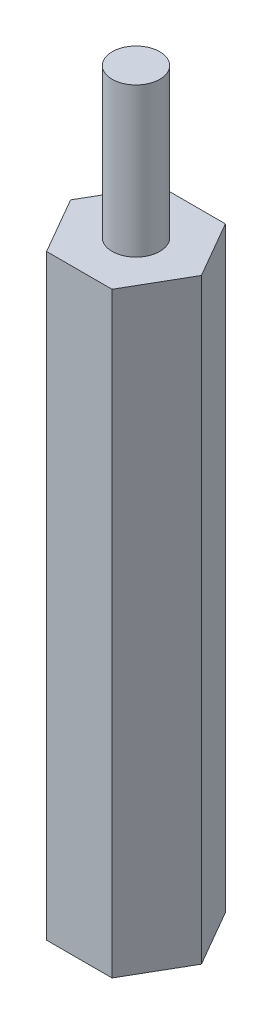
SolidWorks part; units mm, degrees
ref_plane "Front Plane" through (0, 0, 0) normal (0, 0, 1) x (1, 0, 0)
ref_plane "Top Plane" through (0, 0, 0) normal (0, 1, 0) x (1, 0, 0)
ref_plane "Right Plane" through (0, 0, 0) normal (1, 0, 0) x (0, 0, -1)
sketch "Sketch1" plane through (0, 0, 0) normal (0, 1, 0) x (1, 0, 0)
  line L1 (1.3931, -2.413) -> (2.7863, 0)
  line L2 (2.7863, 0) -> (1.3931, 2.413)
  line L3 (1.3931, 2.413) -> (-1.3931, 2.413)
  line L4 (-1.3931, 2.413) -> (-2.7863, 0)
  line L5 (-2.7863, 0) -> (-1.3931, -2.413)
  line L6 (-1.3931, -2.413) -> (1.3931, -2.413)
  circle A0 centre (0, 0) radius 2.413 construction
  point P1 (-2.2265, 1.6751)
  dimension "D1" = 4.826
  dimension "D2" = 0
extrude "Boss-Extrude1" add sketch "Sketch1" along normal blind 25.4
sketch "Sketch2" plane through (0, 25.4, 0) normal (0, 1, 0) x (1, 0, 0)
  circle A0 centre (0, 0) radius 1.016
  dimension "D1" = 2.032
extrude "Boss-Extrude2" add sketch "Sketch2" along normal blind 6.35
sketch "Sketch3" plane through (0, 0, 0) normal (0, -1, 0) x (1, 0, 0)
  circle A0 centre (0, 0) radius 1.016
  dimension "D1" = 2.032
extrude "Cut-Extrude1" cut sketch "Sketch3" against normal blind 6.35
